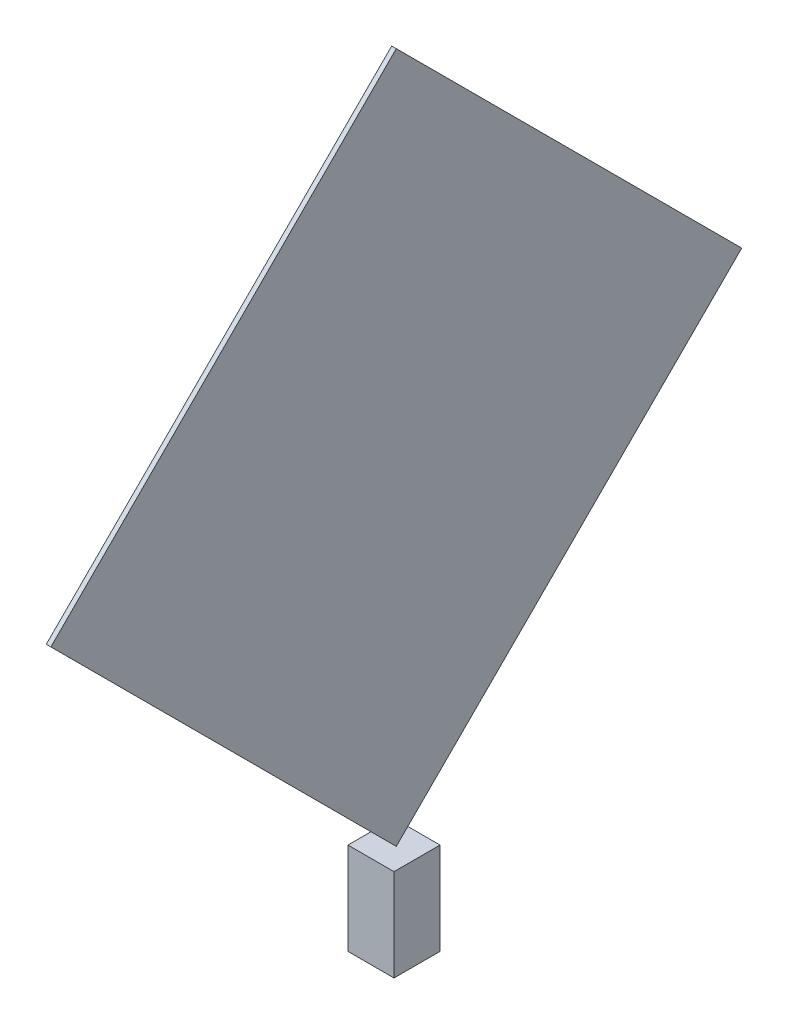
SolidWorks part; units mm, degrees
ref_plane "Front Plane" through (0, 0, 0) normal (0, 0, 1) x (1, 0, 0)
ref_plane "Top Plane" through (0, 0, 0) normal (0, 1, 0) x (1, 0, 0)
ref_plane "Right Plane" through (0, 0, 0) normal (1, 0, 0) x (0, 0, -1)
sketch "Sketch1" plane through (0, 0, 0) normal (0, 1, 0) x (1, 0, 0)
  line L1 (-51.8072, 78.3133) -> (48.1928, 78.3133)
  line L2 (-51.8072, 78.3133) -> (-51.8072, -21.6867)
  line L3 (-51.8072, -21.6867) -> (48.1928, -21.6867)
  line L4 (48.1928, 78.3133) -> (48.1928, -21.6867)
  dimension "D1" = 100
  dimension "D2" = 100
extrude "Boss-Extrude1" add sketch "Sketch1" along normal blind 200
ref_plane "Plane1" through (-1.8072, 0, 0) normal (1, 0, 0) x (0, 0, -1)
sketch "Sketch2" plane through (-1.8072, 0, 0) normal (1, 0, 0) x (0, 0, -1)
  line L0 (-21.6867, 200) -> (78.3133, 200)
  line L2 (78.3133, 200) -> (78.3133, 0)
  line L4 (-21.6867, 0) -> (-21.6867, 200)
  line L5 (-21.6867, 0) -> (-21.6867, 200)
  line L6 (78.3133, 0) -> (-21.6867, 0)
  line L12 (28.3133, 200) -> (778.3133, 950)
  line L13 (28.3133, 200) -> (-721.6867, 950)
  line L14 (778.3133, 950) -> (28.3133, 1700)
  line L15 (-721.6867, 950) -> (28.3133, 1700)
  line L16 (-21.6867, 200) -> (78.3133, 200)
  line L17 (78.3133, 200) -> (78.3133, 0)
  line L18 (78.3133, 0) -> (-21.6867, 0)
  point P0 (0, 0)
  dimension "D2" = 1500
extrude "Boss-Extrude2" add sketch "Sketch2" along normal blind 5 and the other way blind 5 separate body contours L12 L13 L15 L14
